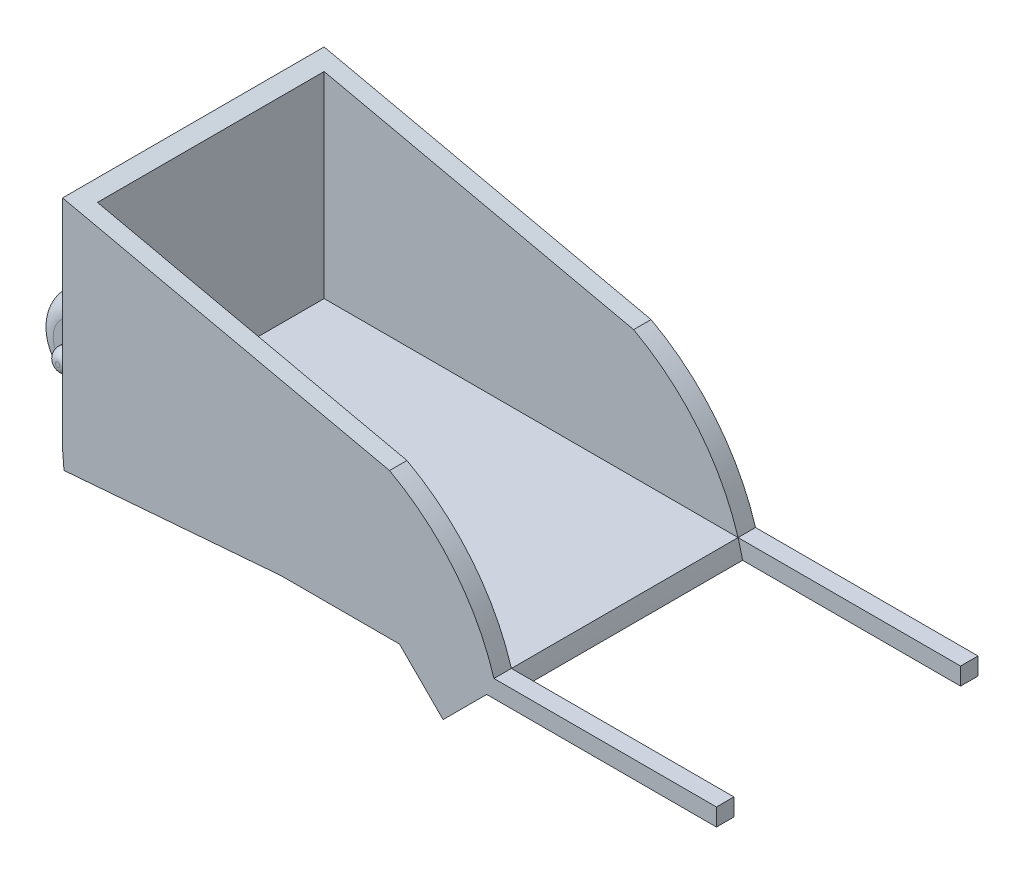
SolidWorks part; units mm, degrees
ref_plane "Front Plane" through (0, 0, 0) normal (0, 0, 1) x (1, 0, 0)
ref_plane "Top Plane" through (0, 0, 0) normal (0, 1, 0) x (1, 0, 0)
ref_plane "Right Plane" through (0, 0, 0) normal (1, 0, 0) x (0, 0, -1)
sketch "Sketch2" plane through (0, 0, 0) normal (0, 1, 0) x (1, 0, 0)
  line L1 (-25, 15) -> (25, 15)
  line L2 (-25, 15) -> (-25, -15)
  line L3 (-25, -15) -> (25, -15)
  line L4 (25, 15) -> (25, -15)
  line L5 (-25, 15) -> (25, -15) construction
  line L6 (-25, -15) -> (25, 15) construction
  point P0 (0, 0)
  dimension "D1" = 50
  dimension "D2" = 30
extrude "Boss-Extrude1" add sketch "Sketch2" along normal blind 25
sketch "Sketch3" plane through (0, 0, 15) normal (0, 0, 1) x (1, 0, 0)
  line L0 (-25, 25) -> (12.5, 16.6667)
  line L2 (-25, 25) -> (25, 25)
  line L3 (25, 25) -> (25, 0)
  arc A0 (12.5, 16.6667) -> (25, 0) centre (0.5688, -5.3026) cw
  dimension "D3" = 25
  dimension "D1" = 37.5
  dimension "D2" = 8.3333
extrude "Cut-Extrude2" cut sketch "Sketch3" against normal through all
ref_plane "Plane1" through (25, 0, 0) normal (-1, 0, 0) x (0, 0, 1)
sketch "Sketch7" plane through (25, 0, 0) normal (-1, 0, 0) x (0, 0, 1)
  line L0 (-15, 25) -> (15, 25) construction
  line L1 (-13, 23) -> (13, 23)
  line L2 (-13, 23) -> (-13, 2)
  line L3 (-13, 2) -> (13, 2)
  line L4 (13, 23) -> (13, 2)
  line L5 (-13, 23) -> (13, 2) construction
  line L6 (-13, 2) -> (13, 23) construction
  line L7 (-15, 25) -> (-15, 0) construction
  line L8 (-15, 0) -> (15, 0) construction
  line L9 (15, 25) -> (15, 0) construction
  point P0 (0, 12.5)
  dimension "D1" = 2
  dimension "D2" = 2
  dimension "D3" = 2
  dimension "D4" = 2
extrude "Cut-Extrude3" cut sketch "Sketch7" along normal blind 48
sketch "Sketch8" plane through (0, 23, 0) normal (0, -1, 0) x (1, 0, 0)
  line L0 (-25, -15) -> (-25, 15) construction
  line L1 (-16, -13) -> (-23, -13)
  line L2 (-16, -13) -> (-16, 13)
  line L3 (-16, 13) -> (-23, 13)
  line L4 (-23, -13) -> (-23, 13)
  line L5 (-25, 15) -> (12.5, 15) construction
  dimension "D1" = 2
  dimension "D2" = 2
extrude "Cut-Extrude6" cut sketch "Sketch8" along normal blind 3 and the other way blind 10
sketch "Sketch9" plane through (25, 0, 0) normal (-1, 0, 0) x (0, 0, 1)
  line L1 (15, 0) -> (13, 0)
  line L2 (15, 0) -> (15, 2)
  line L3 (15, 2) -> (13, 2)
  line L4 (13, 0) -> (13, 2)
  line L5 (-13, 2) -> (-15, 2)
  line L6 (-13, 2) -> (-13, 0)
  line L7 (-13, 0) -> (-15, 0)
  line L8 (-15, 2) -> (-15, 0)
extrude "Boss-Extrude2" add sketch "Sketch9" against normal blind 25 and the other way blind 25 separate body
sketch "Sketch10" plane through (0, 0, 15) normal (0, 0, 1) x (1, 0, 0)
  line L0 (-25, 0) -> (-35.6546, -0.8551)
  line L1 (-35.6546, -0.8551) -> (-35.4946, -2.8487)
  line L2 (-35.4946, -2.8487) -> (-27.3019, -2.1912)
  line L3 (-27.3019, -2.1912) -> (0, 0)
  line L4 (-25, 0) -> (0, 0)
  dimension "D1" = 2
extrude "Boss-Extrude3" add sketch "Sketch10" against normal blind 30
sketch "Sketch11" plane through (-0.16, 1.9936, 0) normal (-0.08, 0.9968, 0) x (0.9968, 0.08, 0)
  line L0 (-24.9199, 15) -> (-35.6087, 0)
  line L1 (-35.6087, 15) -> (-35.6087, -15) construction
  line L2 (-35.6087, 0) -> (-24.9199, -15)
  line L3 (-24.9199, -15) -> (-35.6087, -15)
  line L4 (-35.6087, -15) -> (-35.6087, 15)
  line L5 (-35.6087, 15) -> (-24.9199, 15)
  line M1 (-35.6087, -15) -> (-24.9199, -15)
  line M3 (-24.9199, 15) -> (-35.6087, 15)
  line M4 (-35.6087, 15) -> (-35.6087, -15)
extrude "Cut-Extrude7" cut sketch "Sketch11" against normal blind 30 contours L2 M4 M1 | L0 M3 M4
ref_plane "Plane2" through (0, 0, 0) normal (0, 0, 1) x (-0.08, 0.9968, 0)
sketch "Sketch13" plane through (0, 0, 0) normal (0, 0, 1) x (-0.08, 0.9968, 0)
  line L0 (0, 35.6087) -> (2, 35.6087) construction
  circle A0 centre (1, 35.6087) radius 5
  dimension "D1" = 10
extrude "Boss-Extrude4" add sketch "Sketch13" along normal blind 2.5 and the other way blind 2.5
sketch "Sketch14" plane through (0, 0, 2.5) normal (0, 0, 1) x (1, 0, 0)
  circle A0 centre (-35.5746, -1.8519) radius 1.2575
extrude "Boss-Extrude5" add sketch "Sketch14" along normal blind 2.5 and the other way blind 7.5
fillet "Fillet3" radius 2 1 edges at (-40.5585, -2.2519, 2.5)
fillet "Fillet4" radius 2 1 edges at (-40.5585, -2.2519, -2.5)
fillet "Fillet7" radius 1 1 edges at (-34.3171, -1.8519, 5)
fillet "Fillet8" radius 1 1 edges at (-34.3171, -1.8519, -5)
sketch "Sketch15" plane through (0, 0, 15) normal (0, 0, 1) x (1, 0, 0)
  line L0 (23.6477, 0) -> (18.6477, -5)
  line L1 (0, 0) -> (50, 0) construction
  line L2 (18.6477, -5) -> (13.6477, 0)
  line L3 (13.6477, 0) -> (23.6477, 0)
  dimension "D1" = 10
  dimension "D2" = 90
  dimension "D3" = 5
extrude "Boss-Extrude6" add sketch "Sketch15" against normal blind 5
sketch "Sketch16" plane through (0, 0, -15) normal (0, 0, -1) x (-1, 0, 0)
  line L0 (-23.6477, 0) -> (-18.6477, -5)
  line L1 (-18.6477, -5) -> (-13.6477, 0)
  line L2 (-13.6477, 0) -> (-23.6477, 0)
extrude "Boss-Extrude7" add sketch "Sketch16" against normal blind 5
